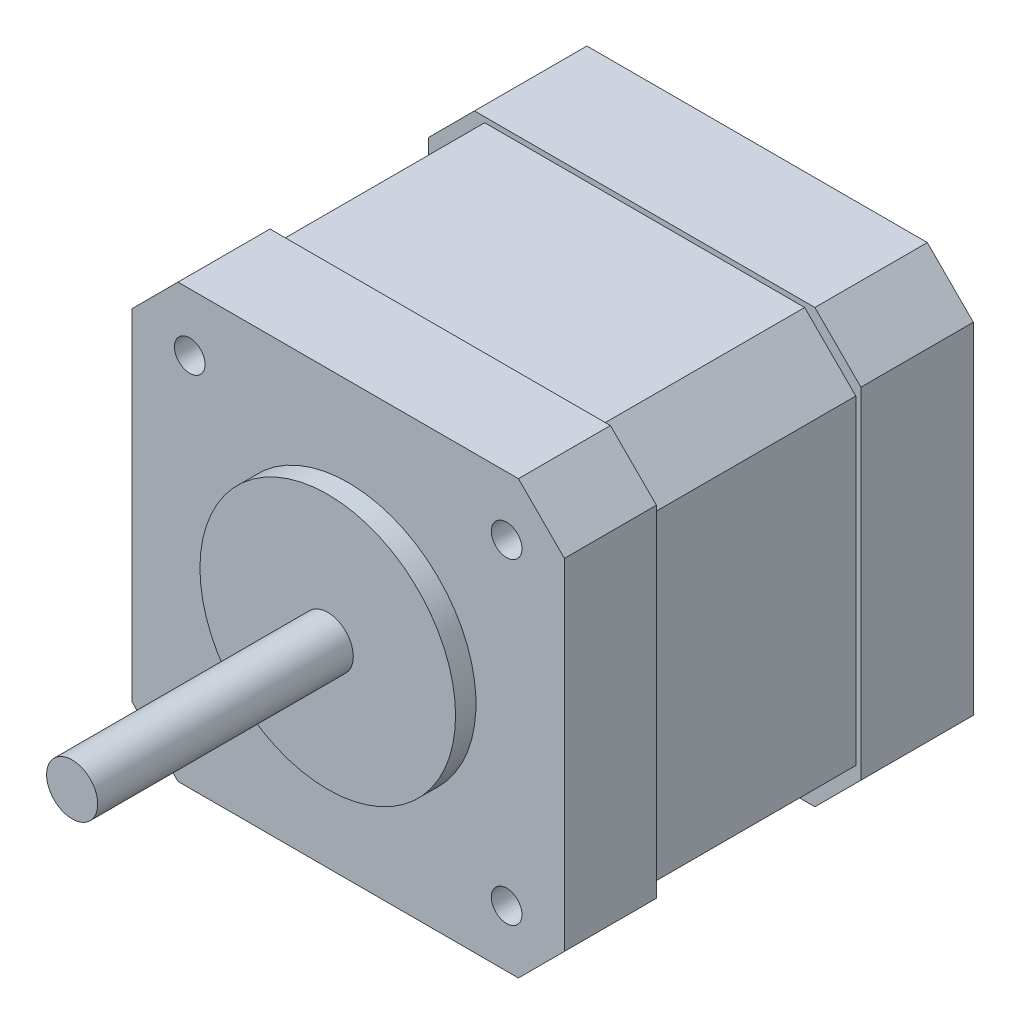
SolidWorks part; units mm, degrees
ref_plane "Plan de face" through (0, 0, 0) normal (0, 0, 1) x (1, 0, 0)
ref_plane "Plan de dessus" through (0, 0, 0) normal (0, 1, 0) x (1, 0, 0)
ref_plane "Plan de droite" through (0, 0, 0) normal (1, 0, 0) x (0, 0, -1)
sketch "Esquisse1" plane through (0, 0, 0) normal (0, 0, 1) x (1, 0, 0)
  line L1 (0, 0) -> (42.3, 0)
  line L2 (0, 0) -> (0, 42.3)
  line L3 (0, 42.3) -> (42.3, 42.3)
  line L4 (42.3, 0) -> (42.3, 42.3)
  dimension "D1" = 42.3
  dimension "D2" = 42.3
extrude "Boss.-Extru.1" add sketch "Esquisse1" along normal blind 11
sketch "Esquisse2" plane through (0, 0, 11) normal (0, 0, 1) x (1, 0, 0)
  line L0 (0, 0) -> (42.3, 0) construction
  line L1 (0.5, 0.5) -> (41.8, 0.5)
  line L2 (0.5, 0.5) -> (0.5, 41.8)
  line L3 (0.5, 41.8) -> (41.8, 41.8)
  line L4 (41.8, 0.5) -> (41.8, 41.8)
  line L5 (0, 42.3) -> (0, 0) construction
  dimension "D1" = 41.3
  dimension "D2" = 41.3
  dimension "D3" = 0.5
  dimension "D4" = 0.5
extrude "Boss.-Extru.2" add sketch "Esquisse2" along normal blind 20
sketch "Esquisse3" plane through (0, 0, 31) normal (0, 0, 1) x (1, 0, 0)
  line L1 (0, 0) -> (42.3, 0)
  line L2 (0, 0) -> (0, 42.3)
  line L3 (0, 42.3) -> (42.3, 42.3)
  line L4 (42.3, 0) -> (42.3, 42.3)
  dimension "D1" = 42.3
  dimension "D2" = 42.3
extrude "Boss.-Extru.3" add sketch "Esquisse3" along normal blind 9
sketch "Esquisse4" plane through (0, 0, 40) normal (0, 0, 1) x (1, 0, 0)
  circle A0 centre (21.15, 21.15) radius 12.5
  dimension "D1" = 25
  dimension "D2" = 21.15
  dimension "D3" = 21.15
extrude "Boss.-Extru.4" add sketch "Esquisse4" along normal blind 2
sketch "Esquisse5" plane through (0, 0, 42) normal (0, 0, 1) x (1, 0, 0)
  circle A0 centre (21.15, 21.15) radius 2.5
  dimension "D1" = 5
  dimension "D2" = 21.15
  dimension "D3" = 21.15
extrude "Boss.-Extru.5" add sketch "Esquisse5" along normal blind 25
sketch "Esquisse6" plane through (0, 0, 40) normal (0, 0, 1) x (1, 0, 0)
  line L0 (0, 0) -> (42.3, 0) construction
  line L1 (0, 42.3) -> (0, 0) construction
  circle A0 centre (5.65, 36.65) radius 1.5
  circle A1 centre (5.65, 5.65) radius 1.5
  circle A2 centre (36.65, 5.5364) radius 1.5
  circle A3 centre (36.65, 36.5364) radius 1.5
  dimension "D1" = 3
  dimension "D2" = 3
  dimension "D3" = 3
  dimension "D4" = 3
  dimension "D5" = 31
  dimension "D6" = 31
  dimension "D7" = 31
  dimension "D8" = 31
  dimension "D9" = 5.65
  dimension "D10" = 5.65
extrude "Enlèv. mat.-Extru.1" cut sketch "Esquisse6" against normal blind 15
chamfer "Chanfrein2" distance 5 angle 45 4 edges at (0.5, 0.5, 21) (41.8, 0.5, 21) (0.5, 41.8, 21) (41.8, 41.8, 21)
chamfer "Chanfrein3" distance 4.5 angle 45 8 edges at (0, 0, 5.5) (0, 0, 35.5) (42.3, 0, 5.5) (42.3, 0, 35.5) (0, 42.3, 35.5) (0, 42.3, 5.5) (42.3, 42.3, 5.5) (42.3, 42.3, 35.5)
